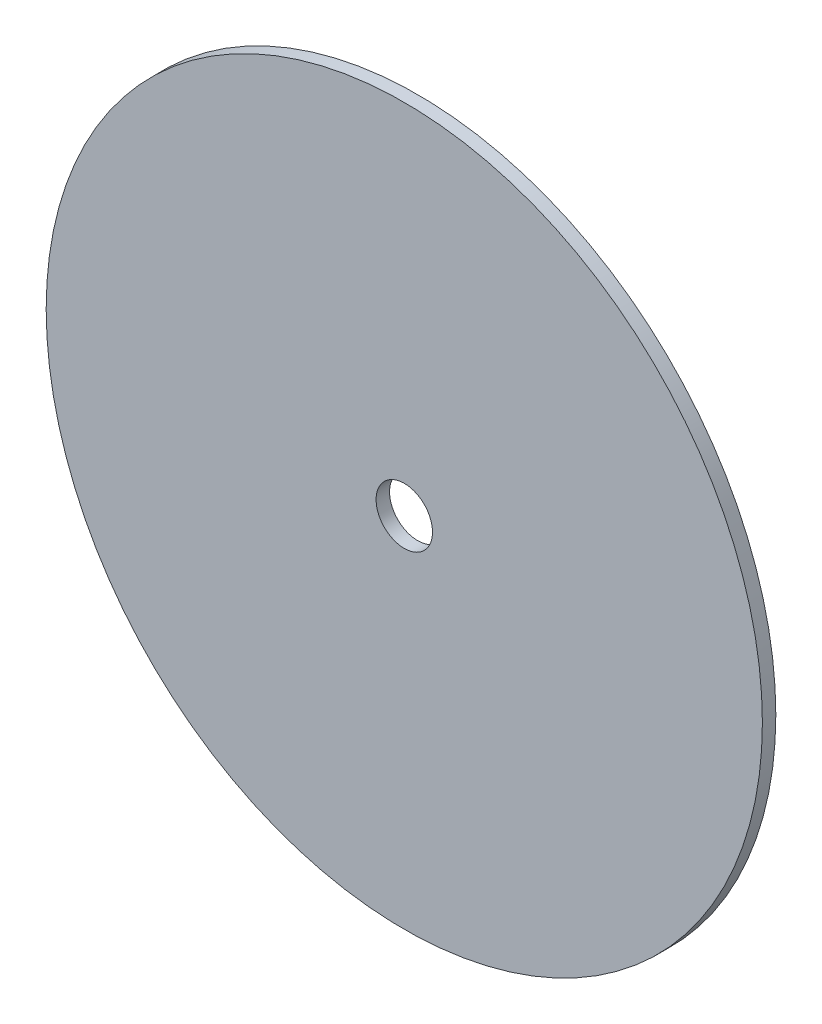
SolidWorks part; units mm, degrees
material "1.0038 (S235JRG2)"
ref_plane "Plan de face" through (0, 0, 0) normal (0, 0, 1) x (1, 0, 0)
ref_plane "Plan de dessus" through (0, 0, 0) normal (0, 1, 0) x (1, 0, 0)
ref_plane "Plan de droite" through (0, 0, 0) normal (1, 0, 0) x (0, 0, -1)
sketch "Esquisse1" plane through (0, 0, 0) normal (0, 0, 1) x (1, 0, 0)
  circle A0 centre (0, 0) radius 12.6
  circle A1 centre (0, 0) radius 160
  dimension "D1" = 320
  dimension "D2" = 25.2
extrude "Boss.-Extru.1" add sketch "Esquisse1" along normal blind 6
